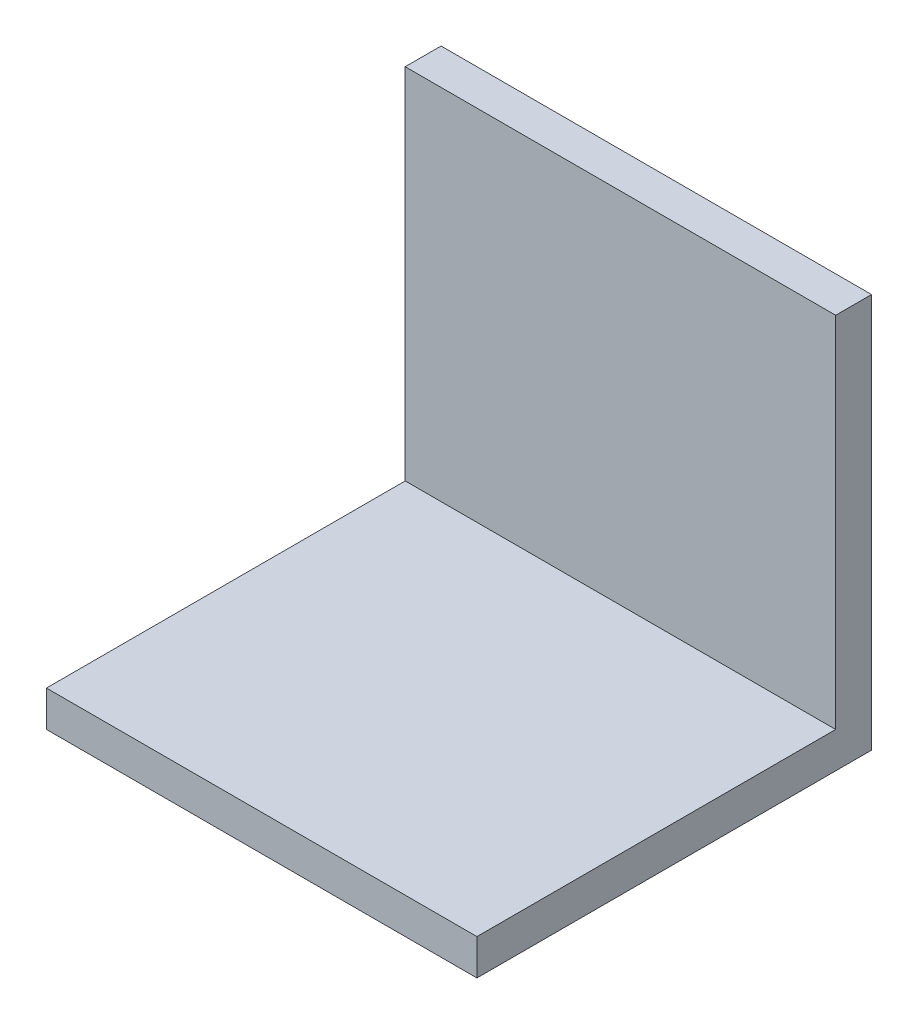
SolidWorks part; units mm, degrees
ref_plane "Front Plane" through (0, 0, 0) normal (0, 0, 1) x (1, 0, 0)
ref_plane "Top Plane" through (0, 0, 0) normal (0, 1, 0) x (1, 0, 0)
ref_plane "Right Plane" through (0, 0, 0) normal (1, 0, 0) x (0, 0, -1)
sketch "Sketch1" plane through (0, 0, 0) normal (0, 0, 1) x (1, 0, 0)
  line L1 (18, 16.5) -> (-18, 16.5)
  line L2 (18, 16.5) -> (18, -16.5)
  line L3 (18, -16.5) -> (-18, -16.5)
  line L4 (-18, 16.5) -> (-18, -16.5)
  line L5 (18, 16.5) -> (-18, -16.5) construction
  line L6 (18, -16.5) -> (-18, 16.5) construction
  point P0 (0, 0)
  dimension "D1" = 36
  dimension "D2" = 33
extrude "Boss-Extrude1" add sketch "Sketch1" along normal blind 3
sketch "Sketch2" plane through (0, 0, 3) normal (0, 0, 1) x (1, 0, 0)
  line L0 (-18, 16.5) -> (-18, -16.5) construction
  line L1 (18, -16.5) -> (-18, -16.5)
  line L2 (18, -16.5) -> (18, -13.5)
  line L3 (18, -13.5) -> (-18, -13.5)
  line L4 (-18, -16.5) -> (-18, -13.5)
  dimension "D1" = 3
extrude "Boss-Extrude2" add sketch "Sketch2" along normal blind 30
